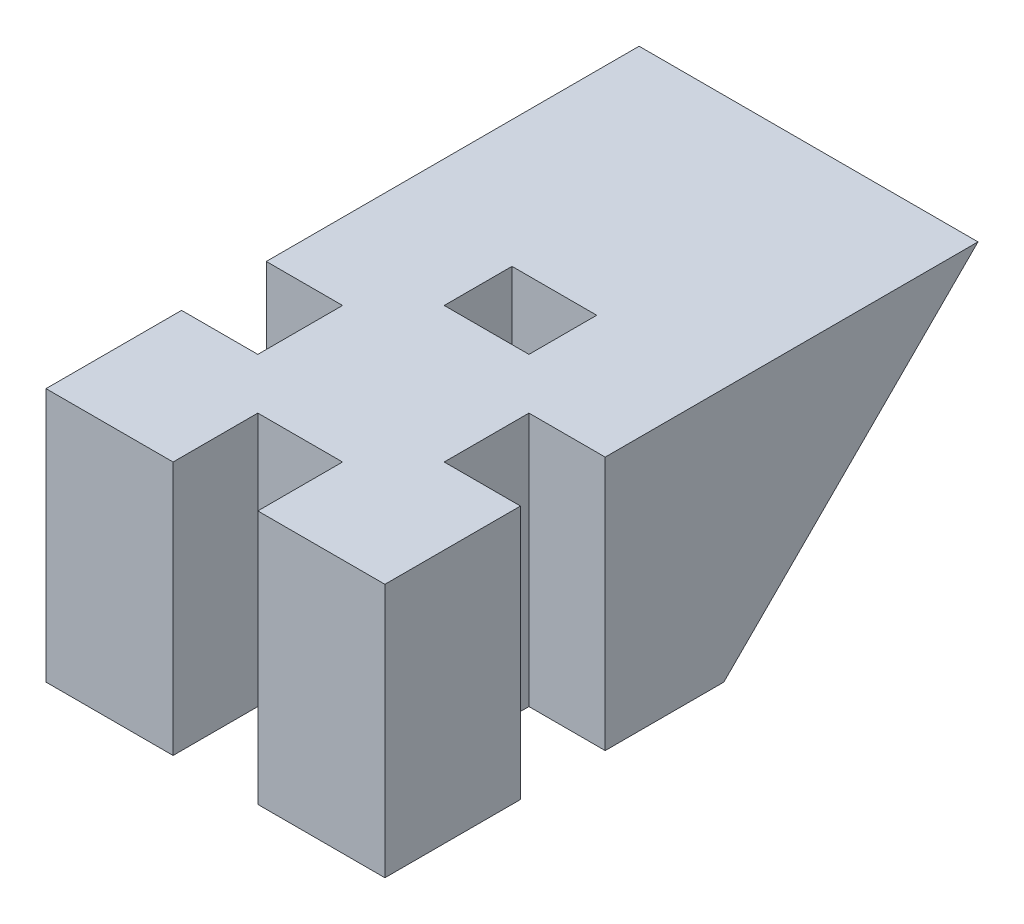
SolidWorks part; units mm, degrees
ref_plane "Front Plane" through (0, 0, 0) normal (0, 0, 1) x (1, 0, 0)
ref_plane "Top Plane" through (0, 0, 0) normal (0, 1, 0) x (1, 0, 0)
ref_plane "Right Plane" through (0, 0, 0) normal (1, 0, 0) x (0, 0, -1)
sketch "Sketch2" plane through (0, 0, 0) normal (0, 1, 0) x (1, 0, 0)
  line L1 (-10, 10) -> (10, 10)
  line L2 (-10, 10) -> (-10, -10)
  line L3 (-10, -10) -> (10, -10)
  line L4 (10, 10) -> (10, -10)
  line L5 (-10, 10) -> (10, -10) construction
  line L6 (-10, -10) -> (10, 10) construction
  point P0 (0, 0)
  dimension "D1" = 20
  dimension "D2" = 20
  dimension "D3" = 20
  dimension "D4" = 20
extrude "Boss-Extrude2" add sketch "Sketch2" along normal blind 40
sketch "Sketch4" plane through (0, 0, 0) normal (0, -1, 0) x (1, 0, 0)
  line L0 (-10, 10) -> (10, 10) construction
  line L1 (-2.5, 15) -> (2.5, 15)
  line L2 (-2.5, 15) -> (-2.5, 5)
  line L3 (-2.5, 5) -> (2.5, 5)
  line L4 (2.5, 15) -> (2.5, 5)
  line L5 (-2.5, 15) -> (2.5, 5) construction
  line L6 (-2.5, 5) -> (2.5, 15) construction
  point P0 (0, 10)
  dimension "D1" = 5
  dimension "D2" = 10
extrude "Cut-Extrude1" cut sketch "Sketch4" against normal through all
pattern_circular "CirPattern1" count 4 over 360 about axis through (0, 0, -0.5) along (0, 1, 0) of "Cut-Extrude1"
sketch "Sketch10" plane through (0, 0, -10) normal (0, 0, -1) x (-1, 0, 0)
  line L0 (10, 40) -> (10, 0) construction
  line L1 (-10, 40) -> (10, 40)
  line L2 (-10, 40) -> (-10, 25)
  line L3 (-10, 25) -> (10, 25)
  line L4 (10, 40) -> (10, 25)
  dimension "D1" = 15
extrude "Boss-Extrude4" add sketch "Sketch10" along normal blind 15
sketch "Sketch12" plane through (-10, 0, 0) normal (-1, 0, 0) x (0, 0, 1)
  line L0 (-25, 40) -> (-10, 25)
  line L1 (-10, 25) -> (-25, 25)
  line L2 (-25, 25) -> (-25, 40)
extrude "Cut-Extrude3" cut sketch "Sketch12" against normal through all
sketch "Sketch13" plane through (-10, 0, 0) normal (-1, 0, 0) x (0, 0, 1)
  line L3 (-10, 25) -> (10, 25)
  line L4 (-10, 25) -> (-10, 0)
  line L5 (-10, 0) -> (10, 0)
  line L6 (10, 25) -> (10, 0)
extrude "Cut-Extrude4" cut sketch "Sketch13" against normal through all
